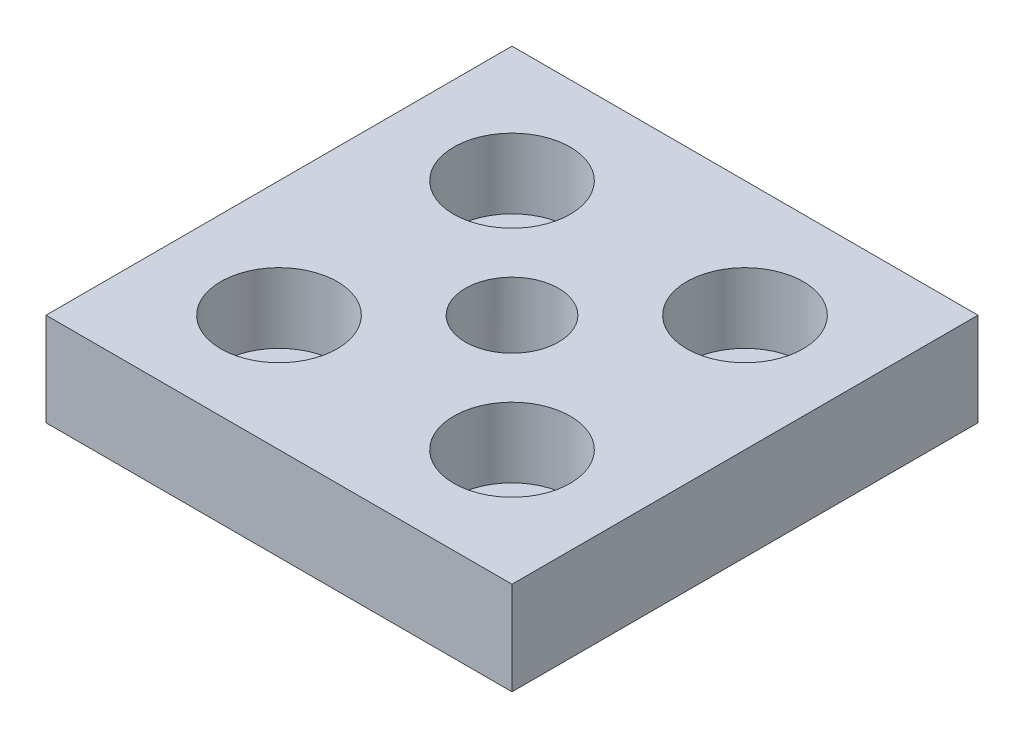
SolidWorks part; units mm, degrees
material "Алюминиевый сплав"
ref_plane "Спереди" through (0, 0, 0) normal (0, 0, 1) x (1, 0, 0)
ref_plane "Сверху" through (0, 0, 0) normal (0, 1, 0) x (1, 0, 0)
ref_plane "Справа" through (0, 0, 0) normal (1, 0, 0) x (0, 0, -1)
sketch "Эскиз1" plane through (0, 0, 0) normal (0, 1, 0) x (1, 0, 0)
  line L1 (-30, -30) -> (30, -30)
  line L2 (-30, -30) -> (-30, 30)
  line L3 (-30, 30) -> (30, 30)
  line L4 (30, -30) -> (30, 30)
  line L5 (-30, -30) -> (30, 30) construction
  line L6 (-30, 30) -> (30, -30) construction
  point P0 (0, 0)
  dimension "D1" = 60
extrude "Бобышка-Вытянуть1" add sketch "Эскиз1" along normal blind 12
hole_wizard "Отверстие обработанное метчиком M141" positions "Эскиз10" profile "Эскиз11" tap size "M14" standard "ISO" end condition up to next
sketch "Эскиз10" plane through (0, 12, 0) normal (0, 1, 0) x (1, 0, 0)
  point P0 (0, 0)
sketch "Эскиз11" plane through (0, 12, 0) normal (1, 0, 0) x (0, 0, 1)
  line L0 (0, 0) -> (0, 12)
  line L1 (0, 12) -> (6, 12)
  line L2 (6, 12) -> (6, 0)
  line L5 (6, 0) -> (0, 0)
  line L11 (0, -6.35) -> (0, 107.95) construction
  dimension "Диаметр проходного сверла" = 12
  dimension "Глубина проходного сверла" = 12
cosmetic thread "Отверстие резьбы4" parameters "D2"=14
sketch "Эскиз12" plane through (0, 12, 0) normal (0, 1, 0) x (1, 0, 0)
  line L1 (15, -15) -> (-15, -15) construction
  line L2 (15, -15) -> (15, 15) construction
  line L3 (15, 15) -> (-15, 15) construction
  line L4 (-15, -15) -> (-15, 15) construction
  line L5 (15, -15) -> (-15, 15) construction
  line L6 (15, 15) -> (-15, -15) construction
  circle A0 centre (-15, 15) radius 4.5
  circle A1 centre (15, 15) radius 4.5
  circle A2 centre (15, -15) radius 4.5
  circle A3 centre (-15, -15) radius 4.5
  point P0 (0, 0)
  dimension "D2" = 9
  dimension "D1" = 30
extrude "Вырез-Вытянуть1" cut sketch "Эскиз12" against normal through all
sketch "Эскиз13" plane through (0, 12, 0) normal (0, 1, 0) x (1, 0, 0)
  circle A0 centre (-15, 15) radius 7.5
  circle A1 centre (15, 15) radius 7.5
  circle A2 centre (15, -15) radius 7.5
  circle A3 centre (-15, -15) radius 7.5
  dimension "D1" = 15
extrude "Вырез-Вытянуть2" cut sketch "Эскиз13" against normal blind 9
